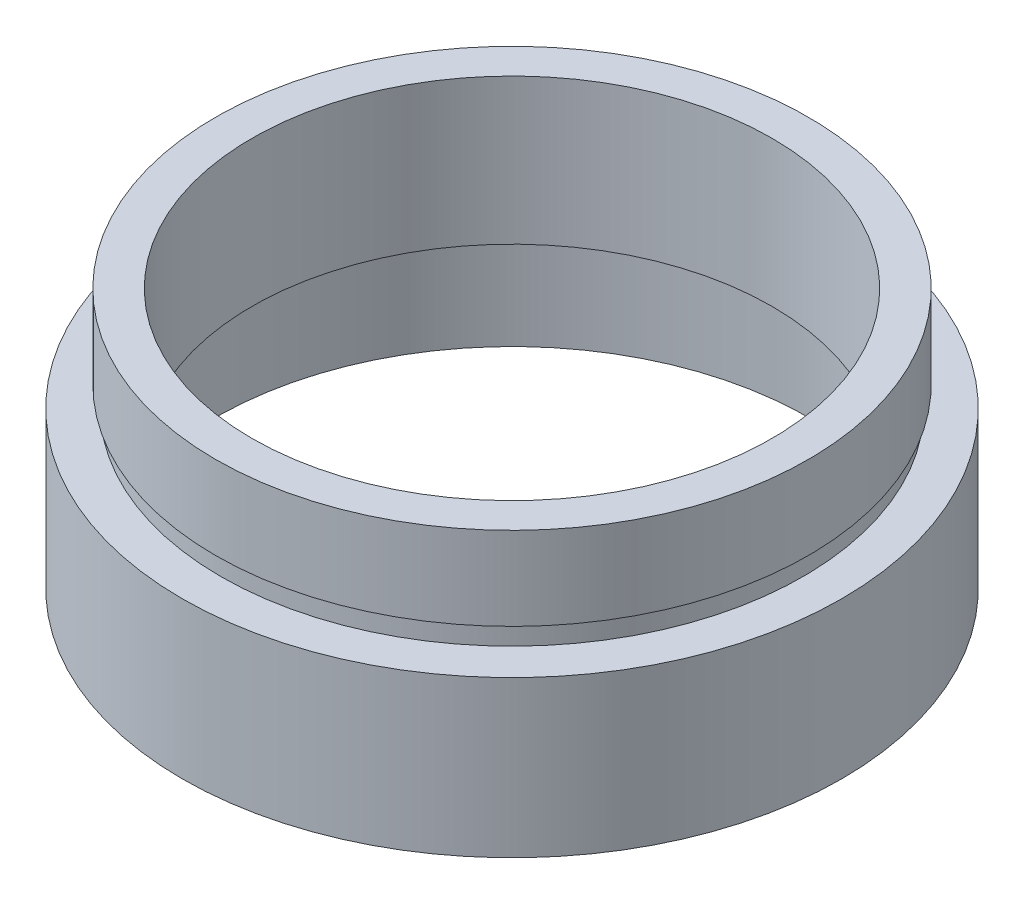
SolidWorks part; units mm, degrees
ref_plane "前视基准面" through (0, 0, 0) normal (0, 0, 1) x (1, 0, 0)
ref_plane "上视基准面" through (0, 0, 0) normal (0, 1, 0) x (1, 0, 0)
ref_plane "右视基准面" through (0, 0, 0) normal (1, 0, 0) x (0, 0, -1)
sketch "草图1" plane through (0, 0, 0) normal (0, 0, 1) x (1, 0, 0)
  line L0 (0, 161.3762) -> (0, 0) construction
  line L1 (141.7365, 0) -> (-131.7984, 0) construction
  line L2 (14.25, 0) -> (14.25, 4.5)
  line L3 (15.85, 0) -> (15.85, 7.5)
  line L4 (14.25, 0) -> (15.85, 0)
  line L5 (14.35, 4.5) -> (14.35, 5.5)
  line L6 (14.25, 4.5) -> (14.35, 4.5)
  line L7 (12.5, 5.5) -> (12.5, 12.5)
  line L8 (12.5, 5.5) -> (14.35, 5.5)
  line L9 (14.25, 12.5) -> (14.25, 8.5)
  line L10 (12.5, 12.5) -> (14.25, 12.5)
  line L11 (14, 8.5) -> (14, 7.5)
  line L12 (14, 8.5) -> (14.25, 8.5)
  line L13 (14, 7.5) -> (15.85, 7.5)
  point P7 (14.25, 2.25)
  dimension "D1" = 14.25
  dimension "D2" = 4.5
  dimension "D3" = 15.85
  dimension "D4" = 14.35
  dimension "D5" = 12.5
  dimension "D6" = 1
  dimension "D7" = 7.5
  dimension "D8" = 14.25
  dimension "D9" = 14
  dimension "D10" = 5
  dimension "D11" = 1
revolve "旋转1" add sketch "草图1" angle 360 about L0
cosmetic thread "装饰螺纹线1" parameters "D2"=28.51
cosmetic thread "装饰螺纹线2" parameters "D2"=26
cosmetic thread "装饰螺纹线3" parameters "D2"=28.49
